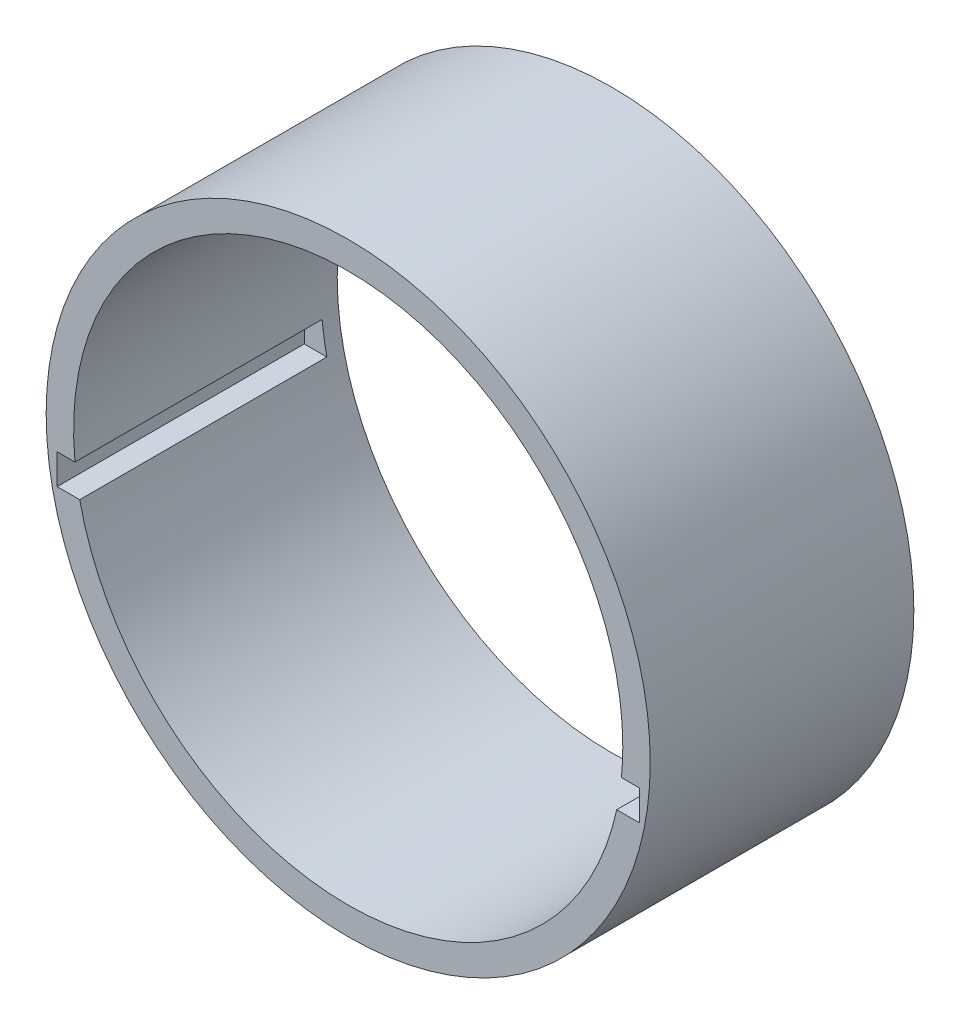
SolidWorks part; units mm, degrees
ref_plane "Front Plane" through (0, 0, 0) normal (0, 0, 1) x (1, 0, 0)
ref_plane "Top Plane" through (0, 0, 0) normal (0, 1, 0) x (1, 0, 0)
ref_plane "Right Plane" through (0, 0, 0) normal (1, 0, 0) x (0, 0, -1)
sketch "Sketch1" plane through (0, 0, 0) normal (0, 0, 1) x (1, 0, 0)
  circle A0 centre (0, 0) radius 55
extrude "Boss-Extrude1" add sketch "Sketch1" along normal blind 48 contours A0
sketch "Sketch2" plane through (0, 0, 48) normal (0, 0, 1) x (1, 0, 0)
  circle A0 centre (0, 0) radius 50
extrude "Cut-Extrude1" cut sketch "Sketch2" against normal through all
sketch "Sketch5" plane through (0, 0, 48) normal (0, 0, 1) x (1, 0, 0)
  line L1 (-53, -10.5) -> (53, -10.5)
  line L2 (-53, -10.5) -> (-53, -5)
  line L3 (-53, -5) -> (53, -5)
  line L4 (53, -10.5) -> (53, -5)
  point P4 (0, 0)
  point P5 (0, 0)
  point P6 (0, 0)
  point P7 (0, 0)
  point P8 (0, 0)
  point P9 (0, 0)
  point P10 (0, 0)
  point P11 (0, 0)
  point P12 (0, 0)
  point P13 (0, 0)
  point P14 (0, 0)
extrude "Cut-Extrude2" cut sketch "Sketch5" against normal blind 45
